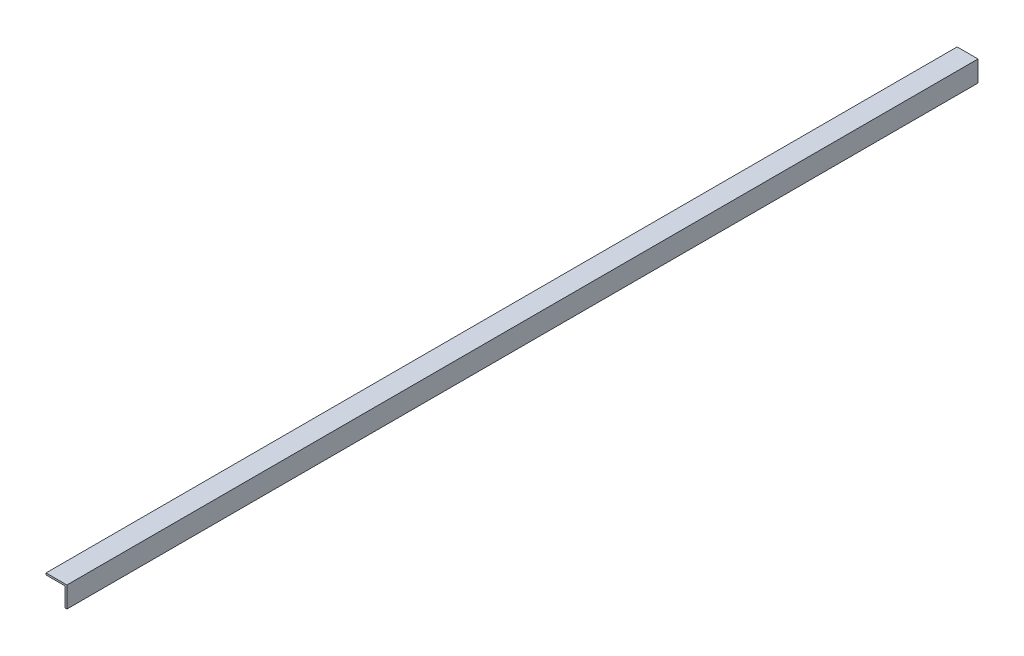
SolidWorks part; units mm, degrees
material "6063-T6"
ref_plane "Front Plane" through (0, 0, 0) normal (0, 0, 1) x (1, 0, 0)
ref_plane "Top Plane" through (0, 0, 0) normal (0, 1, 0) x (1, 0, 0)
ref_plane "Right Plane" through (0, 0, 0) normal (1, 0, 0) x (0, 0, -1)
sketch "Sketch1" plane through (0, 0, 0) normal (0, 0, 1) x (1, 0, 0)
  line L0 (0, 0) -> (-38.1, 0)
  line L1 (-38.1, 0) -> (-38.1, -3.175)
  line L2 (-38.1, -3.175) -> (-3.175, -3.175)
  line L3 (-3.175, -3.175) -> (-3.175, -38.1)
  line L4 (-3.175, -38.1) -> (0, -38.1)
  line L5 (0, -38.1) -> (0, 0)
  dimension "D1" = 38.1
  dimension "D2" = 3.175
extrude "Boss-Extrude1" add sketch "Sketch1" along normal blind 1662.1125
extrude "Cut-Extrude3" [suppressed] cut sketch "Sketch4" against normal blind 44.45
sketch "Sketch4" plane through (10.6701, 3.175, 817.757) normal (0, 1, 0) x (1, 0, 0)
  circle A0 centre (-36.0701, 697.9008) radius 3.9687
pattern_linear "LPattern1" [suppressed] count 15 spacing 101.6
